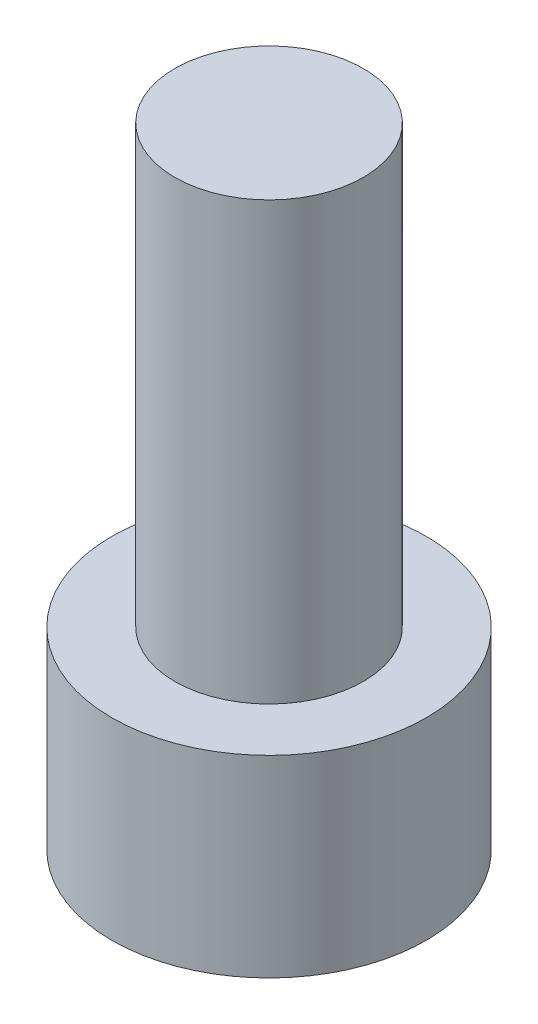
SolidWorks part; units mm, degrees
ref_plane "Front Plane" through (0, 0, 0) normal (0, 0, 1) x (1, 0, 0)
ref_plane "Top Plane" through (0, 0, 0) normal (0, 1, 0) x (1, 0, 0)
ref_plane "Right Plane" through (0, 0, 0) normal (1, 0, 0) x (0, 0, -1)
sketch "Sketch1" plane through (0, 0, 0) normal (0, 1, 0) x (1, 0, 0)
  circle A0 centre (0, 0) radius 2.8575
  dimension "D1" = 5.715
extrude "Boss-Extrude1" add sketch "Sketch1" along normal blind 3.5052
sketch "Sketch2" plane through (0, 0, 0) normal (0, -1, 0) x (1, 0, 0)
  line L1 (1.604, 0) -> (0.802, 1.3891)
  line L2 (0.802, 1.3891) -> (-0.802, 1.3891)
  line L3 (-0.802, 1.3891) -> (-1.604, 0)
  line L4 (-1.604, 0) -> (-0.802, -1.3891)
  line L5 (-0.802, -1.3891) -> (0.802, -1.3891)
  line L6 (0.802, -1.3891) -> (1.604, 0)
  circle A0 centre (0, 0) radius 1.3891 construction
  dimension "D1" = 2.7781
extrude "Cut-Extrude1" cut sketch "Sketch2" against normal blind 1.9558
sketch "Sketch3" plane through (0, 3.5052, 0) normal (0, 1, 0) x (1, 0, 0)
  circle A0 centre (0, 0) radius 1.7145
  dimension "D1" = 3.429
extrude "Boss-Extrude2" add sketch "Sketch3" along normal blind 7.9375
